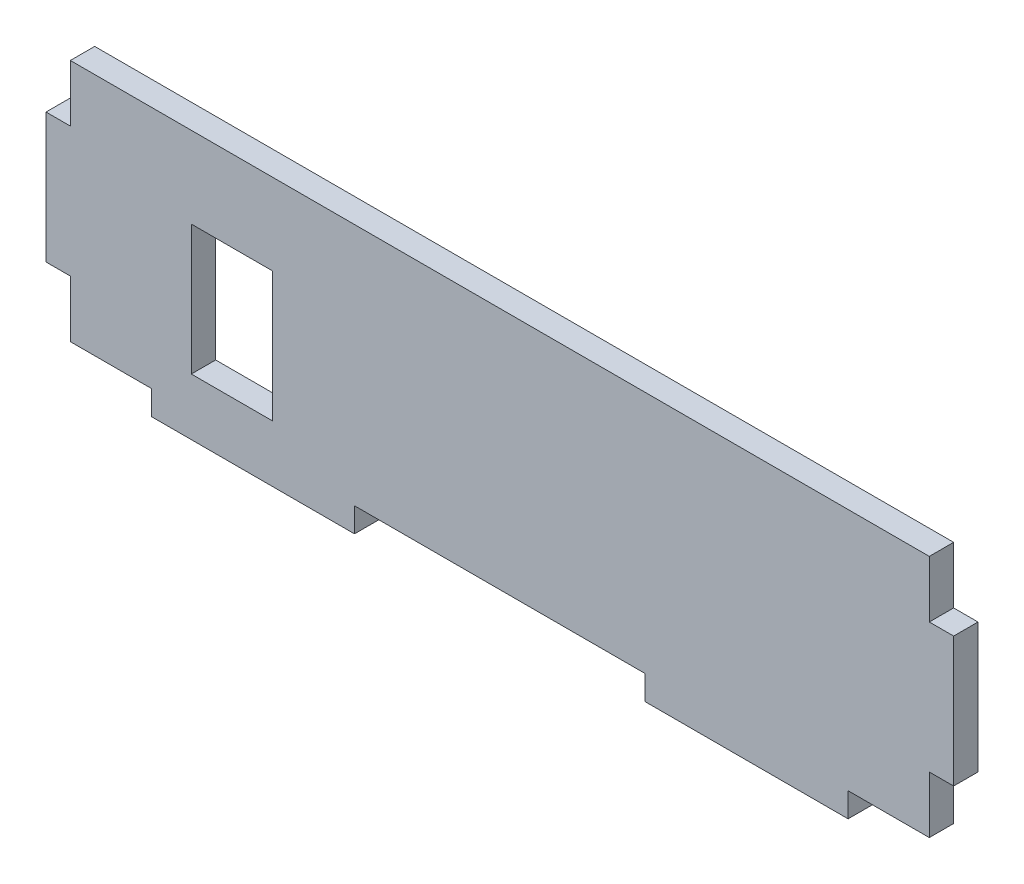
SolidWorks part; units mm, degrees
ref_plane "前视基准面" through (0, 0, 0) normal (0, 0, 1) x (1, 0, 0)
ref_plane "上视基准面" through (0, 0, 0) normal (0, 1, 0) x (1, 0, 0)
ref_plane "右视基准面" through (0, 0, 0) normal (1, 0, 0) x (0, 0, -1)
sketch "草图2" plane through (0, 0, 0) normal (0, 0, 1) x (1, 0, 0)
  line L0 (59.4, 0) -> (77.3, 0)
  line L1 (6.5, 0) -> (16.5, 0)
  line L3 (6.5, 30) -> (112.3, 30)
  line L5 (59.4, 0) -> (41.5, 0)
  line L7 (77.3, 0) -> (77.3, -3)
  line L8 (77.3, -3) -> (102.3, -3)
  line L9 (102.3, 0) -> (102.3, -3)
  line L10 (102.3, 0) -> (112.3, 0)
  line L12 (41.5, 0) -> (41.5, -3)
  line L13 (41.5, -3) -> (16.5, -3)
  line L14 (16.5, 0) -> (16.5, -3)
  line L39 (41.5, 0) -> (77.3, 0)
  line L40 (6.5, 23) -> (6.5, 30)
  line L45 (6.5, 7) -> (3.5, 7)
  line L46 (102.3, 0) -> (112.3, 0)
  line L51 (16.5, 0) -> (6.5, 0)
  line L52 (59.4, 0) -> (41.5, 0)
  line L53 (59.4, 0) -> (77.3, 0)
  line L55 (6.5, 23) -> (3.5, 23)
  line L56 (3.5, 7) -> (3.5, 23)
  line L57 (112.3, 7) -> (112.3, 0)
  line L58 (112.3, 23) -> (112.3, 30)
  line L59 (16.5, 0) -> (21.4, 0)
  line L69 (112.3, 30) -> (112.3, 23)
  line L72 (16.5, 0) -> (41.5, 0) construction
  line L73 (112.3, 23) -> (115.3, 23)
  line L75 (112.3, 7) -> (115.3, 7)
  line L76 (115.3, 23) -> (115.3, 7)
  line L77 (21.4, 0) -> (21.4, 4)
  line L79 (6.5, 7) -> (6.5, 0)
  line L80 (21.4, 4) -> (26.4, 4)
  line L81 (21.4, 4) -> (21.4, 20)
  line L82 (21.4, 20) -> (26.4, 20)
  line L84 (26.4, 4) -> (31.4, 4)
  line L86 (26.4, 20) -> (31.4, 20)
  line L87 (31.4, 4) -> (31.4, 20)
extrude "凸台-拉伸1" add sketch "草图2" along normal blind 3
